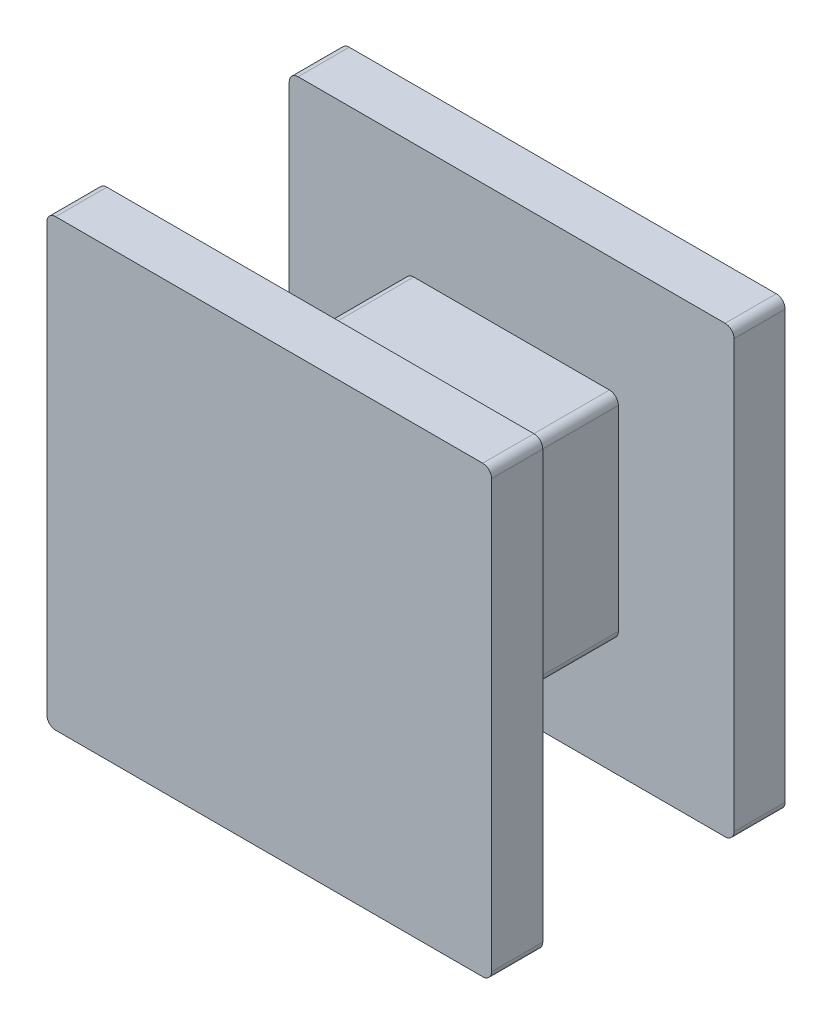
SolidWorks part; units mm, degrees
ref_plane "Front Plane" through (0, 0, 0) normal (0, 0, 1) x (1, 0, 0)
ref_plane "Top Plane" through (0, 0, 0) normal (0, 1, 0) x (1, 0, 0)
ref_plane "Right Plane" through (0, 0, 0) normal (1, 0, 0) x (0, 0, -1)
sketch "Sketch2" plane through (0, 0, 0) normal (0, 0, 1) x (1, 0, 0)
  line L1 (0, 0) -> (4.8, 0)
  line L2 (0, 0) -> (0, -4.8)
  line L3 (0, -4.8) -> (4.8, -4.8)
  line L4 (4.8, 0) -> (4.8, -4.8)
  dimension "D1" = 4.8
  dimension "D2" = 4.8
extrude "Boss-Extrude1" add sketch "Sketch2" along normal blind 4.3
sketch "Sketch3" plane through (0, 0, 4.3) normal (0, 0, 1) x (1, 0, 0)
  line L0 (0, -4.8) -> (4.8, -4.8) construction
  line L1 (-2.6, 2.6) -> (7.4, 2.6)
  line L2 (-2.6, 2.6) -> (-2.6, -7.4)
  line L3 (-2.6, -7.4) -> (7.4, -7.4)
  line L4 (7.4, 2.6) -> (7.4, -7.4)
  line L6 (4.8, -4.8) -> (4.8, 0) construction
  point P6 (2.4, -4.8)
  point P7 (2.4, -7.4)
  point P10 (4.8, -2.4)
  point P11 (7.4, -2.4)
  dimension "D1" = 10
  dimension "D2" = 10
extrude "Boss-Extrude2" add sketch "Sketch3" along normal blind 1.15
sketch "Sketch4" plane through (0, 0, 0) normal (0, 0, -1) x (-1, 0, 0)
  line L0 (2.6, 2.6) -> (2.6, -7.4) construction
  line L1 (-7.4, 2.6) -> (2.6, 2.6)
  line L2 (-7.4, 2.6) -> (-7.4, -7.4)
  line L3 (-7.4, -7.4) -> (2.6, -7.4)
  line L4 (2.6, 2.6) -> (2.6, -7.4)
  line L5 (-7.4, -7.4) -> (-7.4, 2.6) construction
  line L6 (2.6, -7.4) -> (-7.4, -7.4) construction
  line L8 (-7.4, 2.6) -> (2.6, 2.6) construction
extrude "Boss-Extrude4" add sketch "Sketch4" along normal blind 1.15
fillet "Fillet2" radius 0.2 12 edges at (7.4, -7.4, 4.875) (-2.6, -7.4, 4.875) (-2.6, -7.4, -0.575) (7.4, -7.4, -0.575) (4.8, -4.8, 2.15) (0, -4.8, 2.15) (7.4, 2.6, 4.875) (-2.6, 2.6, 4.875) (0, 0, 2.15) (4.8, 0, 2.15) (7.4, 2.6, -0.575) (-2.6, 2.6, -0.575)
